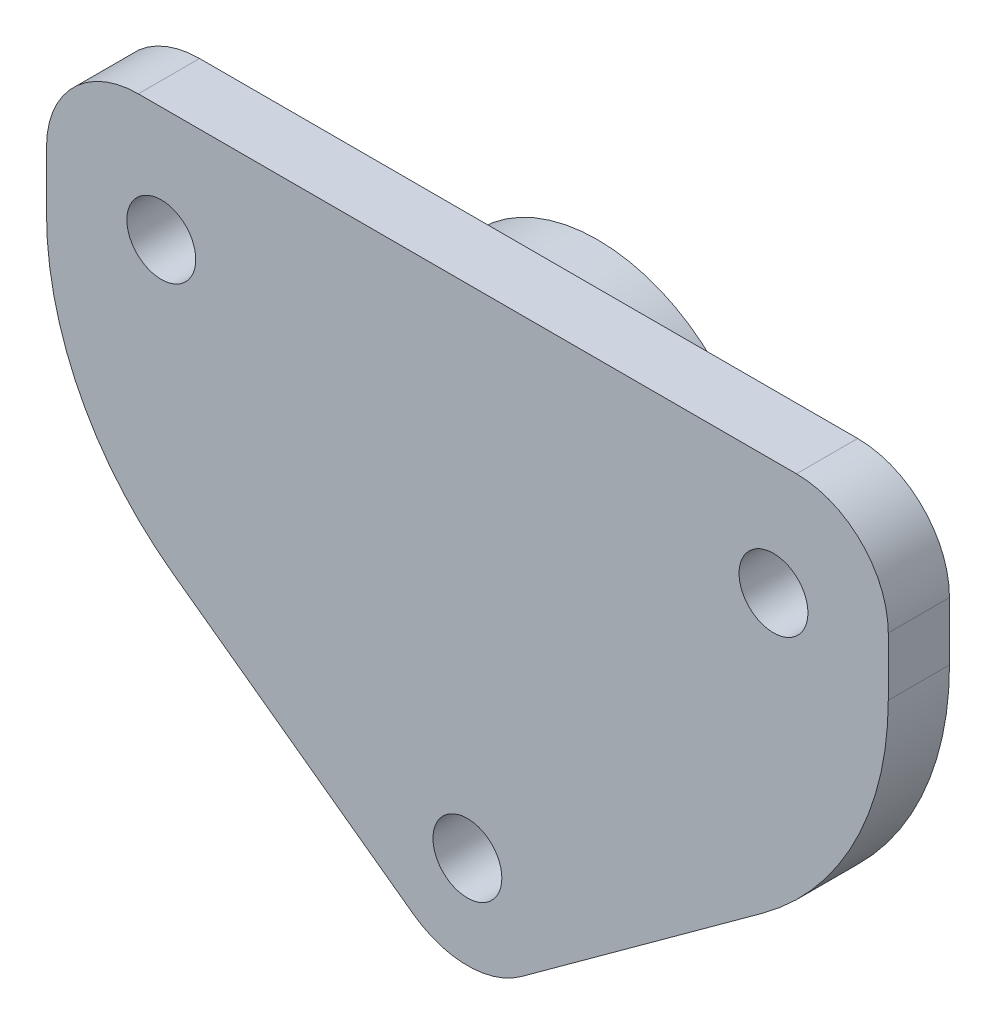
SolidWorks part; units mm, degrees
ref_plane "Plan de face" through (0, 0, 0) normal (0, 0, 1) x (1, 0, 0)
ref_plane "Plan de dessus" through (0, 0, 0) normal (0, 1, 0) x (1, 0, 0)
ref_plane "Plan de droite" through (0, 0, 0) normal (1, 0, 0) x (0, 0, -1)
sketch "Esquisse1" plane through (0, 0, 0) normal (0, 0, 1) x (1, 0, 0)
  line L0 (-55, 20) -> (-27.5, 0)
  line L1 (-55, 40) -> (0, 40)
  line L2 (-55, 40) -> (-55, 20)
  line L4 (0, 40) -> (0, 20)
  line L5 (-27.5, 0) -> (0, 20)
  circle A1 centre (-47.5, 32.5) radius 2.25
  circle A2 centre (-7.5, 32.5) radius 2.25
  circle A3 centre (-27.5, 7.5) radius 2.25
  dimension "D3" = 4.5
  dimension "D4" = 4.5
  dimension "D5" = 4.5
  dimension "D12" = 7.5
  dimension "D13" = 7.5
  dimension "D14" = 7.5
  dimension "D15" = 7.5
  dimension "D1" = 55
  dimension "D2" = 40
extrude "Boss.-Extru.1" add sketch "Esquisse1" along normal blind 4
fillet "Congé2" radius 6 3 edges at (-27.5, 0, 2) (-55, 40, 2) (0, 40, 2)
fillet "Congé3" radius 20 2 edges at (-55, 20, 2) (0, 20, 2)
sketch "Esquisse2" plane through (0, 0, 0) normal (0, 0, -1) x (-1, 0, 0)
  line L0 (0, 30.1845) -> (0, 34) construction
  line L1 (55, 34) -> (55, 30.1845) construction
  circle A0 centre (27.5, 27.5) radius 10.75
  arc A1 (23.971, 2.5666) -> (31.029, 2.5666) centre (27.5, 7.419) ccw construction
  circle A2 centre (27.5, 7.5) radius 2.25 construction
  dimension "D1" = 21.5
  dimension "D2" = 27.5
  dimension "D3" = 27.5
  dimension "D4" = 20
extrude "Boss.-Extru.2" add sketch "Esquisse2" along normal blind 4.5
sketch "Esquisse3" plane through (0, 0, -4.5) normal (0, 0, -1) x (-1, 0, 0)
  line L0 (27.5, 30.25) -> (27.5, 24.75)
  arc A0 (27.5, 30.25) -> (27.5, 24.75) centre (27.5, 27.5) ccw
  dimension "D1" = 5.5
revolve "Enlèvement de matière-Révolution5" cut sketch "Esquisse3" angle 360 about L0
